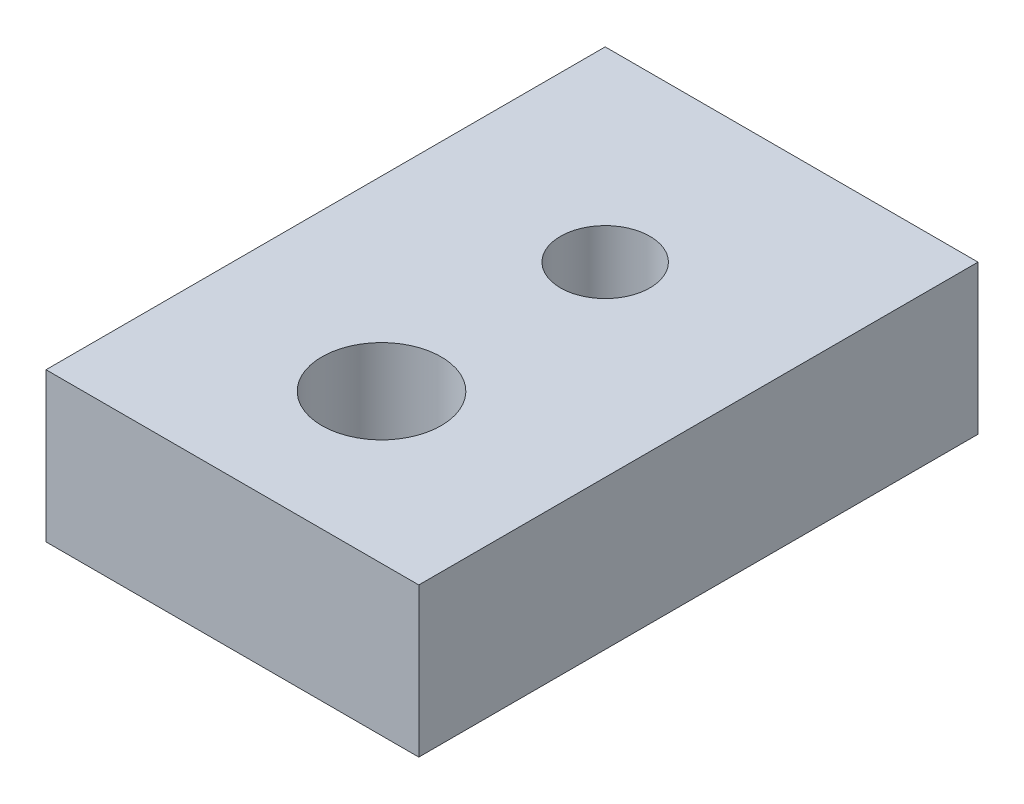
SolidWorks part; units mm, degrees
material "ABS"
ref_plane "Front Plane" through (0, 0, 0) normal (0, 0, 1) x (1, 0, 0)
ref_plane "Top Plane" through (0, 0, 0) normal (0, 1, 0) x (1, 0, 0)
ref_plane "Right Plane" through (0, 0, 0) normal (1, 0, 0) x (0, 0, -1)
sketch "Sketch1" plane through (0, 0, 0) normal (0, 1, 0) x (1, 0, 0)
  line L1 (-25, 25) -> (25, 25)
  line L2 (-25, 25) -> (-25, -50)
  line L3 (-25, -50) -> (25, -50)
  line L4 (25, 25) -> (25, -50)
  circle A0 centre (0, 0) radius 6
  circle A1 centre (0, -30) radius 8
  dimension "D1" = 12
  dimension "D2" = 16
  dimension "D3" = 30
  dimension "D4" = 25
  dimension "D6" = 25
  dimension "D7" = 20
  dimension "D8" = 25
  dimension "D9" = 50
extrude "Boss-Extrude1" add sketch "Sketch1" along normal blind 20
